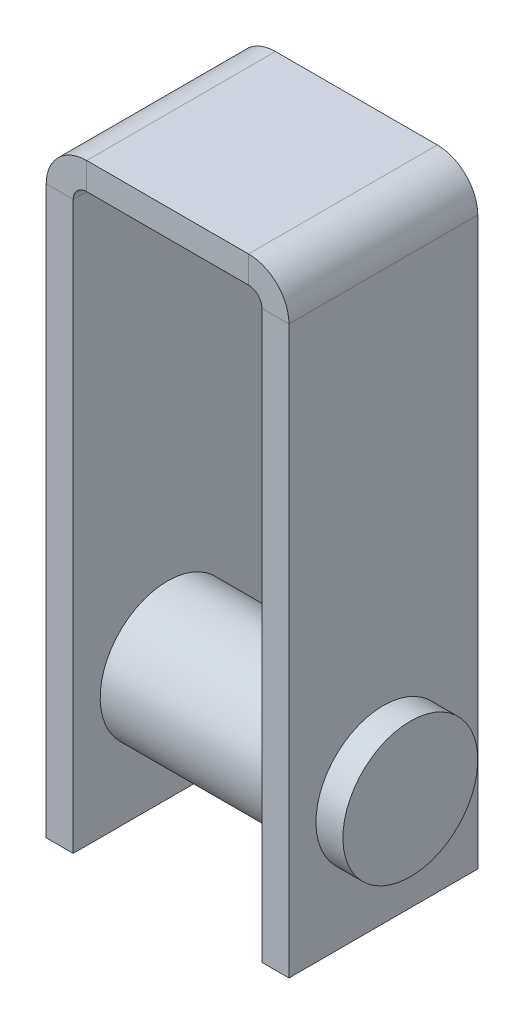
SolidWorks part; units mm, degrees
ref_plane "Front Plane" through (0, 0, 0) normal (0, 0, 1) x (1, 0, 0)
ref_plane "Top Plane" through (0, 0, 0) normal (0, 1, 0) x (1, 0, 0)
ref_plane "Right Plane" through (0, 0, 0) normal (1, 0, 0) x (0, 0, -1)
sketch "Sketch1" plane through (0, 0, 0) normal (0, 0, 1) x (1, 0, 0)
  line L0 (-21.6452, 0) -> (38.3548, 0)
  line L1 (48.3548, -10) -> (48.3548, -220)
  line L2 (-31.6452, -10) -> (-31.6452, -220)
  arc A0 (48.3548, -10) -> (38.3548, 0) centre (38.3548, -10) ccw
  arc A1 (-21.6452, 0) -> (-31.6452, -10) centre (-21.6452, -10) ccw
  point P7 (48.3548, 0)
  point P10 (-31.6452, 0)
  dimension "D4" = 10
  dimension "D1" = 80
  dimension "D2" = 220
  dimension "D3" = 220
sketch "Sketch2" plane through (0, 0, 0) normal (1, 0, 0) x (0, 0, -1)
  line L1 (-35, -5) -> (35, -5)
  line L2 (-35, -5) -> (-35, 5)
  line L3 (-35, 5) -> (35, 5)
  line L4 (35, -5) -> (35, 5)
  line L5 (-35, -5) -> (35, 5) construction
  line L6 (-35, 5) -> (35, -5) construction
  point P0 (0, 0)
  dimension "D1" = 70
  dimension "D2" = 10
sweep "Sweep1" add profiles "Sketch2" path "Sketch1"
sketch "Sketch3" plane through (53.3548, 0, 0) normal (1, 0, 0) x (0, 0, -1)
  line L0 (35, -220) -> (-35, -220) construction
  circle A0 centre (0, -175) radius 25
  dimension "D1" = 45
extrude "Cut-Extrude1" cut sketch "Sketch3" against normal through all
sketch "Sketch4" plane through (53.3548, 0, 0) normal (1, 0, 0) x (0, 0, -1)
  circle A0 centre (0, -175) radius 25
  dimension "D1" = 50
extrude "Boss-Extrude1" add sketch "Sketch4" along normal blind 10 and the other way blind 100
sketch "Sketch5" plane through (0, 5, 0) normal (0, 1, 0) x (1, 0, 0)
  line L0 (8.3548, -35) -> (8.3548, 35) construction
  line L1 (-21.6452, -35) -> (38.3548, -35) construction
  line L2 (-21.6452, 35) -> (38.3548, 35) construction
  line L3 (-21.6452, -15) -> (38.3548, -15) construction
  dimension "D1" = 20
ref_plane "Plane1" through (0, 0, 0) normal (0, 0, 1) x (1, 0, 0)
sketch "Sketch6" plane through (0, 0, 0) normal (0, 0, 1) x (1, 0, 0)
  line L0 (53.3548, -175) -> (23.3548, -175) construction
  line L1 (23.3548, -175) -> (-6.6452, -175) construction
  dimension "D1" = 30
  dimension "D2" = 30
